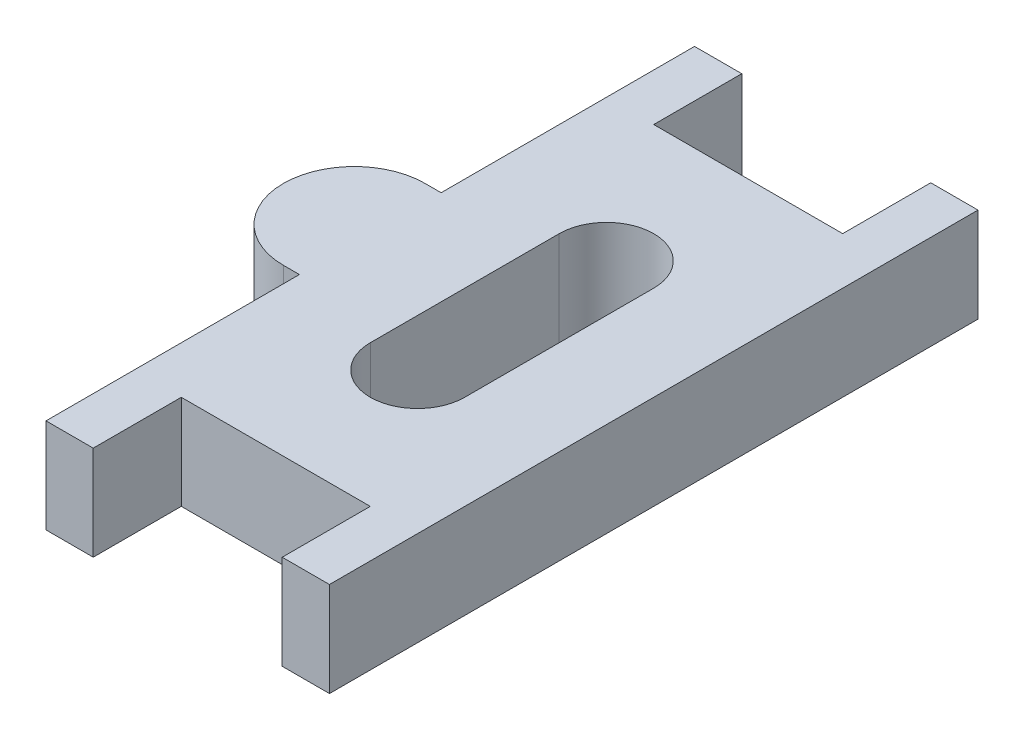
SolidWorks part; units mm, degrees
ref_plane "Front Plane" through (0, 0, 0) normal (0, 0, 1) x (1, 0, 0)
ref_plane "Top Plane" through (0, 0, 0) normal (0, 1, 0) x (1, 0, 0)
ref_plane "Right Plane" through (0, 0, 0) normal (1, 0, 0) x (0, 0, -1)
sketch "Sketch1" plane through (0, 0, 0) normal (0, 1, 0) x (1, 0, 0)
  line L0 (0, -7.9375) -> (0, 7.9375) construction
  line L1 (-4.7625, 10.8966) -> (4.7625, 10.8966)
  line L2 (-4.7625, 10.8966) -> (-4.7625, 7.9375)
  line L3 (-4.7625, 7.9375) -> (4.7625, 7.9375)
  line L4 (4.7625, 10.8966) -> (4.7625, 7.9375)
  line L5 (-4.7625, 10.8966) -> (4.7625, 7.9375) construction
  line L6 (-4.7625, 7.9375) -> (4.7625, 10.8966) construction
  line L7 (-4.7625, -10.8966) -> (4.7625, -10.8966)
  line L8 (-4.7625, -10.8966) -> (-4.7625, -7.9375)
  line L9 (-4.7625, -7.9375) -> (4.7625, -7.9375)
  line L10 (4.7625, -10.8966) -> (4.7625, -7.9375)
  line L11 (-4.7625, -10.8966) -> (4.7625, -7.9375) construction
  line L12 (-4.7625, -7.9375) -> (4.7625, -10.8966) construction
  point P0 (0, 9.417)
  point P5 (0, -9.4171)
  dimension "D1" = 9.525
  dimension "D2" = 2.9591
  dimension "D3" = 15.875
sketch "Sketch2" plane through (0, 0, 0) normal (0, 1, 0) x (1, 0, 0)
  line L0 (-3.175, 10.8966) -> (-3.175, 7.9375)
  line L1 (-4.7625, 10.8966) -> (4.7625, 10.8966) construction
  line L2 (-4.7625, 7.9375) -> (4.7625, 7.9375) construction
  line L3 (-3.175, 7.9375) -> (3.175, 7.9375)
  line L4 (-3.175, 10.8966) -> (-4.7625, 10.8966)
  line L5 (-4.7625, 10.8966) -> (-4.7625, 2.3813)
  line L7 (-5.3022, -2.3813) -> (-4.7625, -2.3813)
  line L8 (0, 0) -> (-7.9375, 0) construction
  line L9 (0, 4.0105) -> (0, -3.3928) construction
  line L10 (0, -7.9375) -> (0, 7.9375) construction
  line L11 (4.7625, 10.8966) -> (4.7625, -10.8966)
  line L12 (3.175, 10.8966) -> (4.7625, 10.8966)
  line L13 (3.175, 10.8966) -> (3.175, 7.9375)
  line L14 (0, -4.0105) -> (0, 3.3928) construction
  line L15 (3.175, -10.8966) -> (3.175, -7.9375)
  line L16 (3.175, -10.8966) -> (4.7625, -10.8966)
  line L17 (-5.3023, 2.3813) -> (-4.7625, 2.3813)
  line L19 (-4.7625, -10.8966) -> (-4.7625, -2.3813)
  line L20 (-3.175, -10.8966) -> (-4.7625, -10.8966)
  line L21 (-3.175, -7.9375) -> (3.175, -7.9375)
  line L22 (-3.175, -10.8966) -> (-3.175, -7.9375)
  arc A0 (-5.3023, 2.3813) -> (-5.3022, -2.3813) centre (-5.3022, 0) ccw
  point P18 (0, 0)
  point P27 (0, 7.9375)
  point P38 (0, -7.9375)
  dimension "D1" = 2.3813
  dimension "D2" = 12.446
  dimension "D3" = 1.5875
extrude "Boss-Extrude1" add sketch "Sketch2" along normal blind 3.175
sketch "Sketch3" plane through (0, 3.175, 0) normal (0, 1, 0) x (1, 0, 0)
  line L0 (0, 3.175) -> (0, -3.175) construction
  line L1 (1.5875, 3.175) -> (1.5875, -3.175)
  line L2 (-1.5875, 3.175) -> (-1.5875, -3.175)
  arc A0 (1.5875, 3.175) -> (-1.5875, 3.175) centre (0, 3.175) ccw
  arc A1 (-1.5875, -3.175) -> (1.5875, -3.175) centre (0, -3.175) ccw
  point P3 (0, 0)
  dimension "D1" = 1.5875
  dimension "D2" = 6.35
extrude "Cut-Extrude1" cut sketch "Sketch3" against normal up to next
